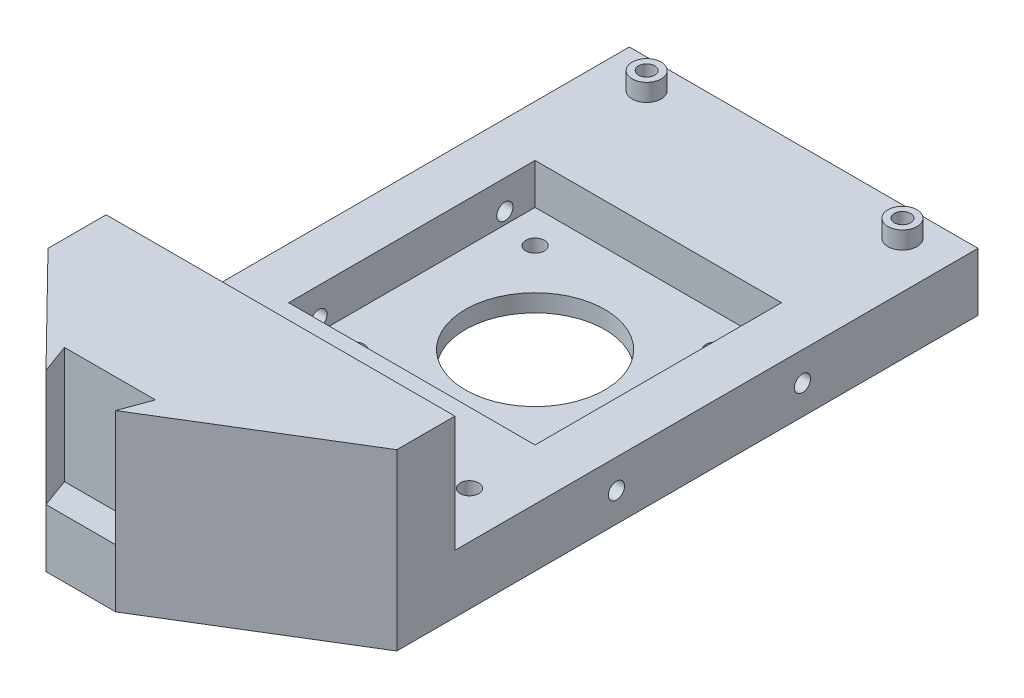
SolidWorks part; units mm, degrees
ref_plane "前视基准面" through (0, 0, 0) normal (0, 0, 1) x (1, 0, 0)
ref_plane "上视基准面" through (0, 0, 0) normal (0, 1, 0) x (1, 0, 0)
ref_plane "右视基准面" through (0, 0, 0) normal (1, 0, 0) x (0, 0, -1)
ref_plane "基准面1" through (0, 30, 0) normal (0, 1, 0) x (1, 0, 0)
sketch "草图1" plane through (0, 30, 0) normal (0, 1, 0) x (1, 0, 0)
  line L0 (6.2408, -61.4221) -> (6.2408, 38.5779)
  line L1 (6.2408, 38.5779) -> (-53.7592, 38.5779)
  line L2 (-53.7592, 38.5779) -> (-53.7592, -61.4221)
  line L8 (-37.579, -74.7675) -> (-21.9393, -74.7675)
  line L13 (-35.7592, -79.7675) -> (-37.579, -74.7675)
  line L14 (-37.579, -74.7675) -> (-21.9393, -74.7675)
  line L15 (-21.9393, -74.7675) -> (-23.7592, -79.7675)
  line L16 (-23.7592, -79.7675) -> (6.2408, -61.4221)
  line L17 (-53.7592, -61.4221) -> (-35.7592, -79.7675)
extrude "凸台-拉伸1" add sketch "草图1" against normal blind 30 contours L2 L17 L13 L8 L15 L16 L0 L1
sketch "草图2" plane through (-53.7592, 0, 0) normal (-1, 0, 0) x (0, 0, 1)
  line L0 (-38.5779, 30) -> (-38.5779, 10)
  line L1 (-38.5779, 10) -> (51.4221, 10)
  line L2 (51.4221, 10) -> (51.4221, 30)
  line L3 (51.4221, 30) -> (-38.5779, 30)
extrude "切除-拉伸1" cut sketch "草图2" against normal through all
sketch "草图3" plane through (0, 10, 0) normal (0, 1, 0) x (-1, 0, 0)
  line L0 (44.9592, 28.8221) -> (2.5592, 28.8221)
  line L1 (2.5592, 28.8221) -> (2.5592, -13.5779)
  line L2 (2.5592, -13.5779) -> (44.9592, -13.5779)
  line L3 (44.9592, -13.5779) -> (44.9592, 28.8221)
extrude "切除-拉伸2" cut sketch "草图3" against normal blind 7
ref_plane "基准面2" through (0, 0, -33.5779) normal (0, 0, 1) x (1, 0, 0)
sketch "草图4" plane through (0, 0, -33.5779) normal (0, 0, 1) x (1, 0, 0)
  line L0 (-43.2592, 13) -> (-45.7592, 13)
  line L1 (-45.7592, 13) -> (-45.7592, 10)
  line L2 (-45.7592, 10) -> (-43.2592, 10)
  line L3 (-43.2592, 10) -> (-43.2592, 13)
  line L4 (-45.7592, 13) -> (-45.7592, 10) construction
revolve "旋转1" add sketch "草图4" angle 360 about L4
sketch "草图5" plane through (0, 0, -33.5779) normal (0, 0, 1) x (1, 0, 0)
  line L0 (0.7408, 13) -> (-1.7592, 13)
  line L1 (-1.7592, 13) -> (-1.7592, 10)
  line L2 (-1.7592, 10) -> (0.7408, 10)
  line L3 (0.7408, 10) -> (0.7408, 13)
  line L4 (-1.7592, 13) -> (-1.7592, 10) construction
revolve "旋转2" add sketch "草图5" angle 360 about L4
hole_wizard "Ø24.0 (24) 直径孔1" positions "草图7" profile "草图6" hole size "Ø24.0" standard "ANSI Metric"
sketch "草图7" plane through (0, 3, 0) normal (0, 1, 0) x (1, 0, 0)
  point P0 (-23.7592, -7.6221)
sketch "草图6" plane through (-23.7592, 3, 7.6221) normal (1, 0, 0) x (0, 0, 1)
  line L0 (0, 0) -> (0, 3)
  line L1 (0, 3) -> (12, 3)
  line L2 (12, 3) -> (12, 0)
  line L5 (12, 0) -> (0, 0)
  line L11 (0, -6.35) -> (0, 107.95) construction
  dimension "通孔孔直径" = 24
  dimension "通孔孔深度" = 3
hole_wizard "Ø3.2 (3.2) 直径孔1" positions "草图9" profile "草图8" hole size "Ø3.2" standard "ANSI Metric"
sketch "草图9" plane through (0, 3, 0) normal (0, 1, 0) x (1, 0, 0)
  point P0 (-8.2592, -23.1221)
  point P1 (-39.2592, 7.8779)
  point P2 (-8.2592, 7.8779)
  point P3 (-39.2592, -23.1221)
sketch "草图8" plane through (-8.2592, 3, 23.1221) normal (1, 0, 0) x (0, 0, 1)
  line L0 (0, 0) -> (0, 3)
  line L1 (0, 3) -> (1.6, 3)
  line L2 (1.6, 3) -> (1.6, 0)
  line L5 (1.6, 0) -> (0, 0)
  line L11 (0, -6.35) -> (0, 107.95) construction
  dimension "通孔孔直径" = 3.2
  dimension "通孔孔深度" = 3
hole_wizard "Ø2.8 (2.8) 直径孔1" positions "草图11" profile "草图10" hole size "Ø2.8" standard "ANSI Metric"
sketch "草图11" plane through (0, 13, 0) normal (0, 1, 0) x (1, 0, 0)
  point P0 (-45.7592, 33.5779)
  point P1 (-1.7592, 33.5779)
sketch "草图10" plane through (-45.7592, 13, -33.5779) normal (1, 0, 0) x (0, 0, 1)
  line L0 (0, 0) -> (0, 13)
  line L1 (0, 13) -> (1.4, 13)
  line L2 (1.4, 13) -> (1.4, 0)
  line L5 (1.4, 0) -> (0, 0)
  line L11 (0, -6.35) -> (0, 107.95) construction
  dimension "通孔孔直径" = 2.8
  dimension "通孔孔深度" = 13
hole_wizard "Ø3.2 (3.2) 直径孔2" positions "草图13" profile "草图12" hole size "Ø3.2" standard "ANSI Metric"
sketch "草图13" plane through (0, 10, 0) normal (0, 1, 0) x (1, 0, 0)
  point P0 (-45.7592, -40.9221)
  point P1 (-1.7592, -40.9221)
sketch "草图12" plane through (-45.7592, 10, 40.9221) normal (1, 0, 0) x (0, 0, 1)
  line L0 (0, 0) -> (0, 10)
  line L1 (0, 10) -> (1.6, 10)
  line L2 (1.6, 10) -> (1.6, 0)
  line L5 (1.6, 0) -> (0, 0)
  line L11 (0, -6.35) -> (0, 107.95) construction
  dimension "通孔孔直径" = 3.2
  dimension "通孔孔深度" = 10
hole_wizard "Ø2.8 (2.8) 直径孔2" positions "草图15" profile "草图14" hole size "Ø2.8" standard "ANSI Metric"
sketch "草图15" plane through (-53.7592, 0, 0) normal (-1, 0, 0) x (0, 0, 1)
  point P0 (-8.3779, 5)
  point P1 (23.6221, 5)
sketch "草图14" plane through (-53.7592, 5, -8.3779) normal (0, 1, 0) x (0, 0, 1)
  line L0 (0, 0) -> (0, 8.8)
  line L1 (0, 8.8) -> (1.4, 8.8)
  line L2 (1.4, 8.8) -> (1.4, 0)
  line L5 (1.4, 0) -> (0, 0)
  line L11 (0, -6.35) -> (0, 107.95) construction
  dimension "通孔孔直径" = 2.8
  dimension "通孔孔深度" = 8.8
hole_wizard "Ø2.8 (2.8) 直径孔3" positions "草图17" profile "草图16" hole size "Ø2.8" standard "ANSI Metric"
sketch "草图17" plane through (-2.5592, 0, 0) normal (-1, 0, 0) x (0, 0, 1)
  point P0 (-8.3779, 5)
  point P1 (23.6221, 5)
sketch "草图16" plane through (-2.5592, 5, -8.3779) normal (0, 1, 0) x (0, 0, 1)
  line L0 (0, 0) -> (0, 8.8)
  line L1 (0, 8.8) -> (1.4, 8.8)
  line L2 (1.4, 8.8) -> (1.4, 0)
  line L5 (1.4, 0) -> (0, 0)
  line L11 (0, -6.35) -> (0, 107.95) construction
  dimension "通孔孔直径" = 2.8
  dimension "通孔孔深度" = 8.8
sketch "草图18" plane through (0, 0, 0) normal (0, -1, 0) x (1, 0, 0)
  line L6 (-35.7592, 79.7675) -> (-37.579, 74.7675)
  line L7 (-37.579, 74.7675) -> (-21.9393, 74.7675)
  line L8 (-21.9393, 74.7675) -> (-23.7592, 79.7675)
  line L9 (-23.7592, 79.7675) -> (-35.7592, 79.7675)
extrude "凸台-拉伸2" add sketch "草图18" against normal blind 10
